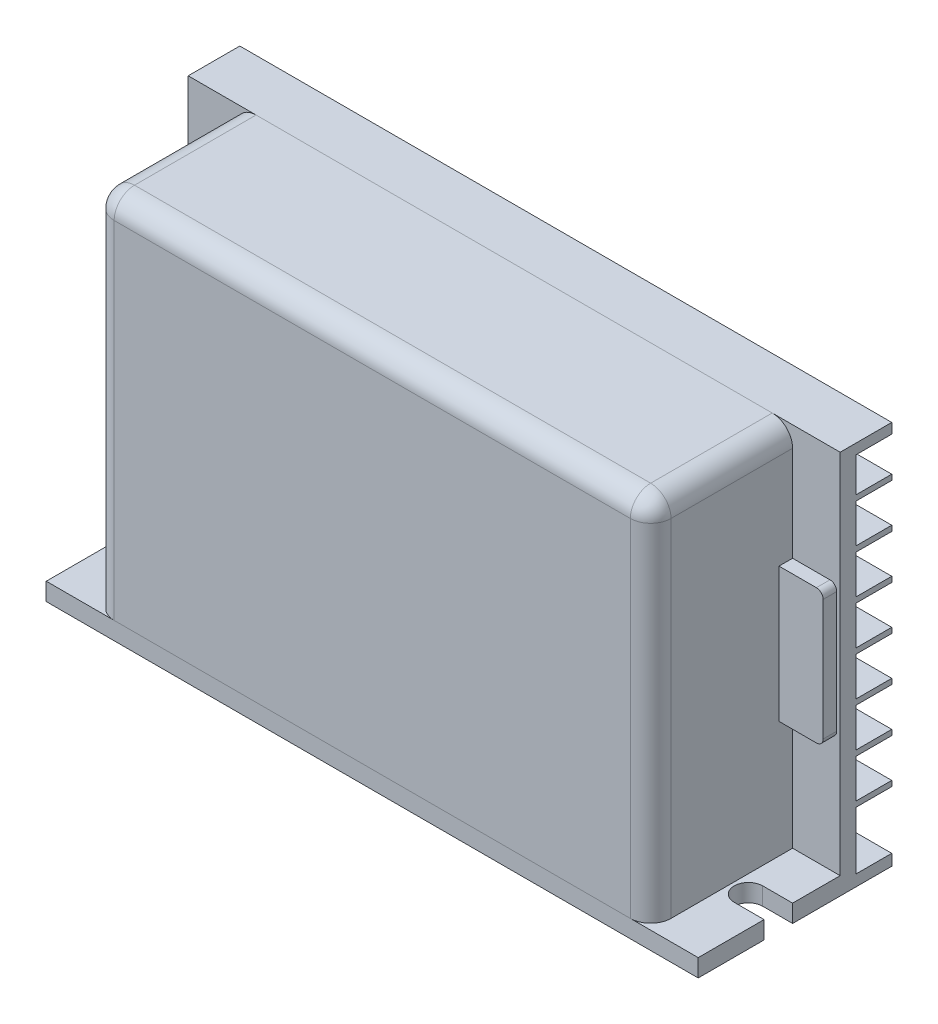
SolidWorks part; units mm, degrees
ref_plane "Plano frontal" through (0, 0, 0) normal (0, 0, 1) x (1, 0, 0)
ref_plane "Plano superior" through (0, 0, 0) normal (0, 1, 0) x (1, 0, 0)
ref_plane "Plano direito" through (0, 0, 0) normal (1, 0, 0) x (0, 0, -1)
sketch "Esboço1" plane through (0, 0, 0) normal (0, 1, 0) x (1, 0, 0)
  line L1 (48, 14.25) -> (-48, 14.25)
  line L2 (48, 14.25) -> (48, -0.35)
  line L3 (48, -14.25) -> (-48, -14.25)
  line L4 (-48, 14.25) -> (-48, -0.35)
  line L5 (48, 14.25) -> (-48, -14.25) construction
  line L6 (48, -14.25) -> (-48, 14.25) construction
  line L7 (48, -4.55) -> (43.6, -4.55)
  line L8 (48, -0.35) -> (43.6, -0.35)
  line L10 (48, -4.55) -> (43.6, -4.55)
  line L13 (48, -4.55) -> (48, -14.25)
  line L14 (48, -0.35) -> (43.6, -0.35)
  line L15 (0, -55) -> (0, 55) construction
  line L17 (-48, -0.35) -> (-43.6, -0.35)
  line L18 (-48, -4.55) -> (-43.6, -4.55)
  line L19 (-48, -4.55) -> (-48, -14.25)
  arc A1 (43.6, -0.35) -> (43.6, -4.55) centre (43.6, -2.45) ccw
  arc A4 (-43.6, -0.35) -> (-43.6, -4.55) centre (-43.6, -2.45) cw
  point P0 (0, 0)
  point P5 (0, 0)
  point P6 (0, 0)
  point P13 (0, 0)
  dimension "D5" = 6.5
  dimension "D1" = 28.5
  dimension "D2" = 96
  dimension "D3" = 4.2
  dimension "D4" = 9.7
extrude "Ressalto-extrusão1" add sketch "Esboço1" along normal blind 2.6 contours L17 A4 L18 L19 L3 L13 L7 A1 L8 L2 L1 L4
sketch "Esboço2" plane through (0, 2.6, 0) normal (0, 1, 0) x (1, 0, 0)
  line L0 (-48, 14.25) -> (-48, -0.35) construction
  line L1 (-48, 8.95) -> (48, 8.95)
  line L2 (-48, 8.95) -> (-48, 6.65)
  line L3 (-48, 6.65) -> (48, 6.65)
  line L4 (48, 8.95) -> (48, 6.65)
  line L5 (48, 14.25) -> (48, -0.35) construction
  line L6 (48, 14.25) -> (-48, 14.25) construction
  dimension "D1" = 5.3
  dimension "D2" = 2.3
extrude "Ressalto-extrusão2" add sketch "Esboço2" along normal blind 54
sketch "Esboço3" plane through (0, 2.6, 0) normal (0, 1, 0) x (1, 0, 0)
  line L4 (-48, 8.95) -> (48, 8.95)
  line L5 (48, 8.95) -> (48, 14.25)
  line L6 (48, 14.25) -> (-48, 14.25)
  line L7 (-48, 14.25) -> (-48, 8.95)
  line L8 (-48, 8.95) -> (48, 8.95)
  line L9 (48, 8.95) -> (48, 14.25)
  line L10 (48, 14.25) -> (-48, 14.25)
  line L11 (-48, 14.25) -> (-48, 8.95)
  dimension "D1" = 0
extrude "Corte-extrusão1" cut sketch "Esboço3" against normal offset from surface (0.95 mm away) 1.65 up to face at (0, 0, 1.6333)
sketch "Esboço4" plane through (0, 0, -8.95) normal (0, 0, -1) x (-1, 0, 0)
  line L0 (48, 56.6) -> (48, 1.65) construction
  line L1 (-48, 56.6) -> (48, 56.6)
  line L2 (-48, 56.6) -> (-48, 55.1)
  line L3 (-48, 55.1) -> (48, 55.1)
  line L4 (48, 56.6) -> (48, 55.1)
  dimension "D1" = 1.5
extrude "Ressalto-extrusão3" add sketch "Esboço4" along normal up to surface (5.3 mm away) up to face at (0, 0.825, -14.25)
sketch "Esboço5" plane through (0, 0, -8.95) normal (0, 0, -1) x (-1, 0, 0)
  line L0 (-48, 50) -> (48, 50)
  line L1 (-48, 55.1) -> (-48, 1.65) construction
  line L2 (48, 55.1) -> (48, 1.65) construction
  line L3 (-48, 55.1) -> (48, 55.1) construction
  line L4 (-48, 43.4917) -> (48, 43.4917)
  line L5 (-48, 36.9833) -> (48, 36.9833)
  line L6 (-48, 30.475) -> (48, 30.475)
  line L7 (-48, 23.9667) -> (48, 23.9667)
  line L8 (-48, 17.4583) -> (48, 17.4583)
  line L9 (-48, 10.95) -> (48, 10.95)
  line L10 (-48, 1.65) -> (48, 1.65) construction
  dimension "D1" = 5.1
  dimension "D3" = 9.3
  dimension "D2" = 7
extrude "Extrusão-Fina1" add sketch "Esboço5" along normal up to surface (5.3 mm away) thin
sketch "Esboço6" plane through (0, 0, -6.65) normal (0, 0, 1) x (1, 0, 0)
  line L0 (-48, 56.6) -> (48, 56.6) construction
  line L1 (-38, 56.6) -> (38, 56.6)
  line L2 (-41, 53.6) -> (-41, 2.6)
  line L3 (-41, 2.6) -> (41, 2.6)
  line L4 (41, 53.6) -> (41, 2.6)
  line L5 (48, 2.6) -> (-48, 2.6) construction
  line L6 (0, 56.6) -> (0, 0) construction
  arc A0 (38, 56.6) -> (41, 53.6) centre (38, 53.6) cw
  arc A1 (-38, 56.6) -> (-41, 53.6) centre (-38, 53.6) ccw
  point P13 (41, 56.6)
  point P16 (-41, 56.6)
  dimension "D2" = 3
  dimension "D1" = 82
extrude "Ressalto-extrusão4" add sketch "Esboço6" along normal up to surface (20.9 mm away) separate body up to face at (0, 1.3, 14.25)
fillet "Filete1" radius 3 5 edges at (-41, 28.1, 14.25) (-40.1213, 55.7213, 14.25) (0, 56.6, 14.25) (40.1213, 55.7213, 14.25) (41, 28.1, 14.25)
sketch "Esboço7" plane through (-41, 0, 0) normal (-1, 0, 0) x (0, 0, 1)
  line L0 (4.55, 0) -> (14.25, 0) construction
  line L1 (1.15, 40.5) -> (10.85, 40.5)
  line L2 (1.15, 40.5) -> (1.15, 21.8)
  line L3 (1.15, 21.8) -> (10.85, 21.8)
  line L4 (10.85, 40.5) -> (10.85, 21.8)
  line L5 (14.25, 53.6) -> (14.25, 2.6) construction
  dimension "D1" = 18.7
  dimension "D2" = 9.7
  dimension "D3" = 21.8
  dimension "D4" = 3.4
extrude "Corte-extrusão2" cut sketch "Esboço7" against normal blind 10
sketch "Esboço8" plane through (0, 0, -6.65) normal (0, 0, 1) x (1, 0, 0)
  line L1 (-46.5, 39.575) -> (-41, 39.575)
  line L2 (-47.5, 38.575) -> (-47.5, 20.775)
  line L3 (-46.5, 19.775) -> (-41, 19.775)
  line L4 (-41, 39.575) -> (-41, 19.775)
  line L9 (-47.5, 29.675) -> (47.5, 29.675) construction
  line L10 (-48, 56.6) -> (-48, 2.6) construction
  line L11 (48, 56.6) -> (48, 2.6) construction
  line L12 (0, -15.675) -> (0, 15.675) construction
  line L13 (46.5, 19.775) -> (41, 19.775)
  line L14 (41, 39.575) -> (41, 19.775)
  line L15 (46.5, 39.575) -> (41, 39.575)
  line L16 (47.5, 38.575) -> (47.5, 20.775)
  arc A0 (-47.5, 20.775) -> (-46.5, 19.775) centre (-46.5, 20.775) ccw
  arc A1 (-46.5, 39.575) -> (-47.5, 38.575) centre (-46.5, 38.575) ccw
  arc A2 (47.5, 20.775) -> (46.5, 19.775) centre (46.5, 20.775) cw
  arc A3 (46.5, 39.575) -> (47.5, 38.575) centre (46.5, 38.575) cw
  point P10 (-45.8948, 29.6)
  point P16 (-47.5, 19.775)
  point P19 (-47.5, 39.575)
  dimension "D2" = 1
  dimension "D1" = 19.8
  dimension "D3" = 7
  dimension "D4" = 0.5
  dimension "D5" = 0.5
extrude "Ressalto-extrusão5" add sketch "Esboço8" along normal blind 2 separate body
